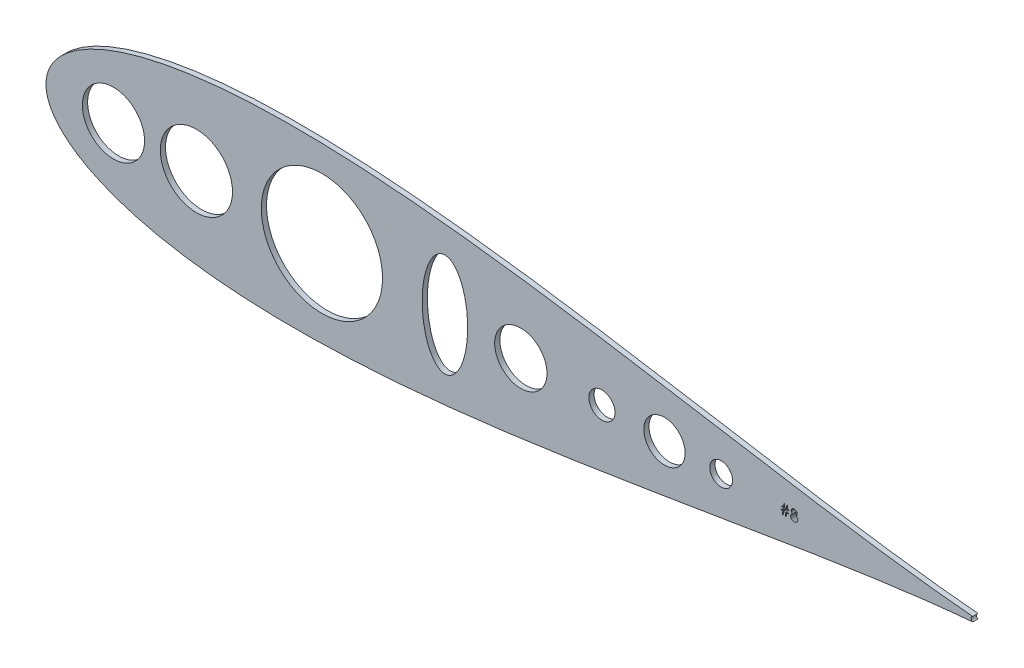
SolidWorks part; units mm, degrees
ref_plane "Front Plane" through (0, 0, 0) normal (0, 0, 1) x (1, 0, 0)
ref_plane "Top Plane" through (0, 0, 0) normal (0, 1, 0) x (1, 0, 0)
ref_plane "Right Plane" through (0, 0, 0) normal (1, 0, 0) x (0, 0, -1)
sketch "Model" plane through (0, 0, 0) normal (0, 0, 1) x (1, 0, 0)
  line L0 (694.3768, 545.3653) -> (694.3768, 545.0397)
  line L1 (694.3768, 545.0397) -> (693.406, 545.0397)
  line L2 (693.406, 545.0397) -> (693.1424, 543.2812)
  line L3 (693.1424, 543.2812) -> (692.7486, 543.2812)
  line L4 (692.7486, 543.2812) -> (693.0121, 545.0397)
  line L5 (693.0121, 545.0397) -> (691.9731, 545.0397)
  line L6 (691.9731, 545.0397) -> (691.7096, 543.2812)
  line L7 (691.7096, 543.2812) -> (691.3158, 543.2812)
  line L8 (691.3158, 543.2812) -> (691.5793, 545.0397)
  line L9 (691.5793, 545.0397) -> (690.7296, 545.0397)
  line L10 (690.7296, 545.0397) -> (690.7296, 545.3653)
  line L11 (690.7296, 545.3653) -> (691.6282, 545.3653)
  line L12 (691.6282, 545.3653) -> (691.8042, 546.5376)
  line L13 (691.8042, 546.5376) -> (690.8599, 546.5376)
  line L14 (690.8599, 546.5376) -> (690.8599, 546.8632)
  line L15 (690.8599, 546.8632) -> (691.8531, 546.8632)
  line L16 (691.8531, 546.8632) -> (692.0973, 548.4915)
  line L17 (692.0973, 548.4915) -> (692.4901, 548.4915)
  line L18 (692.4901, 548.4915) -> (692.2459, 546.8632)
  line L19 (692.2459, 546.8632) -> (693.2859, 546.8632)
  line L20 (693.2859, 546.8632) -> (693.5301, 548.4915)
  line L21 (693.5301, 548.4915) -> (693.9229, 548.4915)
  line L22 (693.9229, 548.4915) -> (693.6787, 546.8632)
  line L23 (693.6787, 546.8632) -> (694.507, 546.8632)
  line L24 (694.507, 546.8632) -> (694.507, 546.5376)
  line L25 (694.507, 546.5376) -> (693.6298, 546.5376)
  line L26 (693.6298, 546.5376) -> (693.4548, 545.3653)
  line L27 (693.4548, 545.3653) -> (694.3768, 545.3653)
  line L28 (693.237, 546.5376) -> (692.197, 546.5376)
  line L29 (692.197, 546.5376) -> (692.022, 545.3653)
  line L30 (692.022, 545.3653) -> (693.061, 545.3653)
  line L31 (693.061, 545.3653) -> (693.237, 546.5376)
  line L32 (697.8235, 546.1112) -> (697.9476, 546.0451)
  line L33 (697.9476, 546.0451) -> (698.0626, 545.9769)
  line L34 (698.0626, 545.9769) -> (698.1685, 545.9057)
  line L35 (698.1685, 545.9057) -> (698.2662, 545.8334)
  line L36 (698.2662, 545.8334) -> (698.3557, 545.7581)
  line L37 (698.3557, 545.7581) -> (698.4361, 545.6797)
  line L38 (698.4361, 545.6797) -> (698.5073, 545.6004)
  line L39 (698.5073, 545.6004) -> (698.5704, 545.5179)
  line L40 (698.5704, 545.5179) -> (698.6254, 545.4335)
  line L41 (698.6254, 545.4335) -> (698.6732, 545.346)
  line L42 (698.6732, 545.346) -> (698.7139, 545.2554)
  line L43 (698.7139, 545.2554) -> (698.7465, 545.1628)
  line L44 (698.7465, 545.1628) -> (698.7729, 545.0661)
  line L45 (698.7729, 545.0661) -> (698.7913, 544.9674)
  line L46 (698.7913, 544.9674) -> (698.8014, 544.8656)
  line L47 (698.8014, 544.8656) -> (698.8055, 544.7608)
  line L48 (698.8055, 544.7608) -> (698.7994, 544.6143)
  line L49 (698.7994, 544.6143) -> (698.7811, 544.4718)
  line L50 (698.7811, 544.4718) -> (698.7516, 544.3334)
  line L51 (698.7516, 544.3334) -> (698.7098, 544.2001)
  line L52 (698.7098, 544.2001) -> (698.6549, 544.0699)
  line L53 (698.6549, 544.0699) -> (698.5887, 543.9457)
  line L54 (698.5887, 543.9457) -> (698.5114, 543.8246)
  line L55 (698.5114, 543.8246) -> (698.4208, 543.7086)
  line L56 (698.4208, 543.7086) -> (698.2967, 543.5783)
  line L57 (698.2967, 543.5783) -> (698.1603, 543.4644)
  line L58 (698.1603, 543.4644) -> (698.0107, 543.3687)
  line L59 (698.0107, 543.3687) -> (697.8479, 543.2904)
  line L60 (697.8479, 543.2904) -> (697.6729, 543.2293)
  line L61 (697.6729, 543.2293) -> (697.4856, 543.1855)
  line L62 (697.4856, 543.1855) -> (697.2852, 543.1601)
  line L63 (697.2852, 543.1601) -> (697.0725, 543.1509)
  line L64 (697.0725, 543.1509) -> (696.8679, 543.1591)
  line L65 (696.8679, 543.1591) -> (696.6756, 543.1815)
  line L66 (696.6756, 543.1815) -> (696.4955, 543.2201)
  line L67 (696.4955, 543.2201) -> (696.3296, 543.2731)
  line L68 (696.3296, 543.2731) -> (696.1749, 543.3423)
  line L69 (696.1749, 543.3423) -> (696.0345, 543.4267)
  line L70 (696.0345, 543.4267) -> (695.9063, 543.5254)
  line L71 (695.9063, 543.5254) -> (695.7903, 543.6404)
  line L72 (695.7903, 543.6404) -> (695.6875, 543.7646)
  line L73 (695.6875, 543.7646) -> (695.599, 543.8918)
  line L74 (695.599, 543.8918) -> (695.5247, 544.022)
  line L75 (695.5247, 544.022) -> (695.4626, 544.1553)
  line L76 (695.4626, 544.1553) -> (695.4148, 544.2917)
  line L77 (695.4148, 544.2917) -> (695.3812, 544.4311)
  line L78 (695.3812, 544.4311) -> (695.3608, 544.5736)
  line L79 (695.3608, 544.5736) -> (695.3537, 544.7191)
  line L80 (695.3537, 544.7191) -> (695.3578, 544.826)
  line L81 (695.3578, 544.826) -> (695.369, 544.9298)
  line L82 (695.369, 544.9298) -> (695.3873, 545.0305)
  line L83 (695.3873, 545.0305) -> (695.4127, 545.1292)
  line L84 (695.4127, 545.1292) -> (695.4463, 545.2249)
  line L85 (695.4463, 545.2249) -> (695.487, 545.3175)
  line L86 (695.487, 545.3175) -> (695.5348, 545.408)
  line L87 (695.5348, 545.408) -> (695.5898, 545.4956)
  line L88 (695.5898, 545.4956) -> (695.6539, 545.581)
  line L89 (695.6539, 545.581) -> (695.7262, 545.6635)
  line L90 (695.7262, 545.6635) -> (695.8086, 545.7439)
  line L91 (695.8086, 545.7439) -> (695.9002, 545.8222)
  line L92 (695.9002, 545.8222) -> (695.9999, 545.8985)
  line L93 (695.9999, 545.8985) -> (696.1098, 545.9718)
  line L94 (696.1098, 545.9718) -> (696.2279, 546.043)
  line L95 (696.2279, 546.043) -> (696.3561, 546.1112)
  line L96 (696.3561, 546.1112) -> (696.1821, 546.212)
  line L97 (696.1821, 546.212) -> (696.0314, 546.3249)
  line L98 (696.0314, 546.3249) -> (695.9042, 546.4481)
  line L99 (695.9042, 546.4481) -> (695.7994, 546.5834)
  line L100 (695.7994, 546.5834) -> (695.718, 546.7269)
  line L101 (695.718, 546.7269) -> (695.661, 546.8755)
  line L102 (695.661, 546.8755) -> (695.6254, 547.0291)
  line L103 (695.6254, 547.0291) -> (695.6142, 547.1879)
  line L104 (695.6142, 547.1879) -> (695.6264, 547.3497)
  line L105 (695.6264, 547.3497) -> (695.6631, 547.5094)
  line L106 (695.6631, 547.5094) -> (695.7251, 547.6682)
  line L107 (695.7251, 547.6682) -> (695.8106, 547.8239)
  line L108 (695.8106, 547.8239) -> (695.9185, 547.9714)
  line L109 (695.9185, 547.9714) -> (696.0447, 548.1017)
  line L110 (696.0447, 548.1017) -> (696.1892, 548.2157)
  line L111 (696.1892, 548.2157) -> (696.353, 548.3134)
  line L112 (696.353, 548.3134) -> (696.5301, 548.3917)
  line L113 (696.5301, 548.3917) -> (696.7143, 548.4467)
  line L114 (696.7143, 548.4467) -> (696.9046, 548.4803)
  line L115 (696.9046, 548.4803) -> (697.103, 548.4915)
  line L116 (697.103, 548.4915) -> (697.2964, 548.4803)
  line L117 (697.2964, 548.4803) -> (697.4816, 548.4467)
  line L118 (697.4816, 548.4467) -> (697.6597, 548.3897)
  line L119 (697.6597, 548.3897) -> (697.8306, 548.3113)
  line L120 (697.8306, 548.3113) -> (697.9894, 548.2136)
  line L121 (697.9894, 548.2136) -> (698.1288, 548.0986)
  line L122 (698.1288, 548.0986) -> (698.2509, 547.9684)
  line L123 (698.2509, 547.9684) -> (698.3547, 547.8219)
  line L124 (698.3547, 547.8219) -> (698.4381, 547.6662)
  line L125 (698.4381, 547.6662) -> (698.4972, 547.5054)
  line L126 (698.4972, 547.5054) -> (698.5328, 547.3415)
  line L127 (698.5328, 547.3415) -> (698.545, 547.1736)
  line L128 (698.545, 547.1736) -> (698.5338, 547.0088)
  line L129 (698.5338, 547.0088) -> (698.5002, 546.8531)
  line L130 (698.5002, 546.8531) -> (698.4432, 546.7065)
  line L131 (698.4432, 546.7065) -> (698.3649, 546.5692)
  line L132 (698.3649, 546.5692) -> (698.2631, 546.4409)
  line L133 (698.2631, 546.4409) -> (698.14, 546.3229)
  line L134 (698.14, 546.3229) -> (697.9924, 546.212)
  line L135 (697.9924, 546.212) -> (697.8235, 546.1112)
  line L136 (697.0776, 547.9704) -> (696.9707, 547.9664)
  line L137 (696.9707, 547.9664) -> (696.869, 547.9562)
  line L138 (696.869, 547.9562) -> (696.7723, 547.9379)
  line L139 (696.7723, 547.9379) -> (696.6797, 547.9124)
  line L140 (696.6797, 547.9124) -> (696.5911, 547.8788)
  line L141 (696.5911, 547.8788) -> (696.5087, 547.8392)
  line L142 (696.5087, 547.8392) -> (696.4304, 547.7913)
  line L143 (696.4304, 547.7913) -> (696.3561, 547.7364)
  line L144 (696.3561, 547.7364) -> (696.2889, 547.6763)
  line L145 (696.2889, 547.6763) -> (696.2309, 547.6143)
  line L146 (696.2309, 547.6143) -> (696.1821, 547.5491)
  line L147 (696.1821, 547.5491) -> (696.1414, 547.4809)
  line L148 (696.1414, 547.4809) -> (696.1108, 547.4097)
  line L149 (696.1108, 547.4097) -> (696.0884, 547.3364)
  line L150 (696.0884, 547.3364) -> (696.0742, 547.2601)
  line L151 (696.0742, 547.2601) -> (696.0701, 547.1807)
  line L152 (696.0701, 547.1807) -> (696.0752, 547.1014)
  line L153 (696.0752, 547.1014) -> (696.0895, 547.0251)
  line L154 (696.0895, 547.0251) -> (696.1129, 546.9497)
  line L155 (696.1129, 546.9497) -> (696.1475, 546.8765)
  line L156 (696.1475, 546.8765) -> (696.1902, 546.8052)
  line L157 (696.1902, 546.8052) -> (696.2431, 546.735)
  line L158 (696.2431, 546.735) -> (696.3052, 546.6679)
  line L159 (696.3052, 546.6679) -> (696.3774, 546.6017)
  line L160 (696.3774, 546.6017) -> (696.4558, 546.5407)
  line L161 (696.4558, 546.5407) -> (696.5382, 546.4877)
  line L162 (696.5382, 546.4877) -> (696.6227, 546.444)
  line L163 (696.6227, 546.444) -> (696.7112, 546.4074)
  line L164 (696.7112, 546.4074) -> (696.8028, 546.3789)
  line L165 (696.8028, 546.3789) -> (696.8974, 546.3585)
  line L166 (696.8974, 546.3585) -> (696.9951, 546.3463)
  line L167 (696.9951, 546.3463) -> (697.0959, 546.3422)
  line L168 (697.0959, 546.3422) -> (697.2251, 546.3493)
  line L169 (697.2251, 546.3493) -> (697.3513, 546.3717)
  line L170 (697.3513, 546.3717) -> (697.4734, 546.4084)
  line L171 (697.4734, 546.4084) -> (697.5925, 546.4592)
  line L172 (697.5925, 546.4592) -> (697.7034, 546.5234)
  line L173 (697.7034, 546.5234) -> (697.8011, 546.5987)
  line L174 (697.8011, 546.5987) -> (697.8856, 546.6841)
  line L175 (697.8856, 546.6841) -> (697.9578, 546.7808)
  line L176 (697.9578, 546.7808) -> (698.0148, 546.8836)
  line L177 (698.0148, 546.8836) -> (698.0565, 546.9854)
  line L178 (698.0565, 546.9854) -> (698.081, 547.0881)
  line L179 (698.081, 547.0881) -> (698.0891, 547.1909)
  line L180 (698.0891, 547.1909) -> (698.085, 547.2632)
  line L181 (698.085, 547.2632) -> (698.0728, 547.3334)
  line L182 (698.0728, 547.3334) -> (698.0525, 547.4016)
  line L183 (698.0525, 547.4016) -> (698.024, 547.4698)
  line L184 (698.024, 547.4698) -> (697.9873, 547.5359)
  line L185 (697.9873, 547.5359) -> (697.9436, 547.6)
  line L186 (697.9436, 547.6) -> (697.8907, 547.6631)
  line L187 (697.8907, 547.6631) -> (697.8296, 547.7252)
  line L188 (697.8296, 547.7252) -> (697.7614, 547.7822)
  line L189 (697.7614, 547.7822) -> (697.6861, 547.832)
  line L190 (697.6861, 547.832) -> (697.6027, 547.8748)
  line L191 (697.6027, 547.8748) -> (697.5121, 547.9094)
  line L192 (697.5121, 547.9094) -> (697.4144, 547.9358)
  line L193 (697.4144, 547.9358) -> (697.3096, 547.9552)
  line L194 (697.3096, 547.9552) -> (697.1977, 547.9664)
  line L195 (697.1977, 547.9664) -> (697.0776, 547.9704)
  line L196 (697.1071, 545.8212) -> (696.9717, 545.8161)
  line L197 (696.9717, 545.8161) -> (696.8425, 545.7998)
  line L198 (696.8425, 545.7998) -> (696.7183, 545.7744)
  line L199 (696.7183, 545.7744) -> (696.6003, 545.7378)
  line L200 (696.6003, 545.7378) -> (696.4873, 545.6899)
  line L201 (696.4873, 545.6899) -> (696.3795, 545.6319)
  line L202 (696.3795, 545.6319) -> (696.2777, 545.5637)
  line L203 (696.2777, 545.5637) -> (696.1821, 545.4854)
  line L204 (696.1821, 545.4854) -> (696.0945, 545.3999)
  line L205 (696.0945, 545.3999) -> (696.0192, 545.3114)
  line L206 (696.0192, 545.3114) -> (695.9551, 545.2188)
  line L207 (695.9551, 545.2188) -> (695.9032, 545.1231)
  line L208 (695.9032, 545.1231) -> (695.8615, 545.0234)
  line L209 (695.8615, 545.0234) -> (695.833, 544.9206)
  line L210 (695.833, 544.9206) -> (695.8157, 544.8137)
  line L211 (695.8157, 544.8137) -> (695.8096, 544.7038)
  line L212 (695.8096, 544.7038) -> (695.8198, 544.5675)
  line L213 (695.8198, 544.5675) -> (695.8493, 544.4362)
  line L214 (695.8493, 544.4362) -> (695.8992, 544.307)
  line L215 (695.8992, 544.307) -> (695.9684, 544.1828)
  line L216 (695.9684, 544.1828) -> (696.0559, 544.0668)
  line L217 (696.0559, 544.0668) -> (696.1597, 543.9661)
  line L218 (696.1597, 543.9661) -> (696.2787, 543.8775)
  line L219 (696.2787, 543.8775) -> (696.4141, 543.8043)
  line L220 (696.4141, 543.8043) -> (696.5637, 543.7463)
  line L221 (696.5637, 543.7463) -> (696.7234, 543.7055)
  line L222 (696.7234, 543.7055) -> (696.8954, 543.6801)
  line L223 (696.8954, 543.6801) -> (697.0776, 543.672)
  line L224 (697.0776, 543.672) -> (697.22, 543.6771)
  line L225 (697.22, 543.6771) -> (697.3544, 543.6923)
  line L226 (697.3544, 543.6923) -> (697.4816, 543.7178)
  line L227 (697.4816, 543.7178) -> (697.6006, 543.7534)
  line L228 (697.6006, 543.7534) -> (697.7126, 543.7982)
  line L229 (697.7126, 543.7982) -> (697.8174, 543.8541)
  line L230 (697.8174, 543.8541) -> (697.9151, 543.9192)
  line L231 (697.9151, 543.9192) -> (698.0046, 543.9956)
  line L232 (698.0046, 543.9956) -> (698.085, 544.078)
  line L233 (698.085, 544.078) -> (698.1552, 544.1645)
  line L234 (698.1552, 544.1645) -> (698.2153, 544.254)
  line L235 (698.2153, 544.254) -> (698.2631, 544.3467)
  line L236 (698.2631, 544.3467) -> (698.3008, 544.4423)
  line L237 (698.3008, 544.4423) -> (698.3282, 544.542)
  line L238 (698.3282, 544.542) -> (698.3445, 544.6448)
  line L239 (698.3445, 544.6448) -> (698.3496, 544.7517)
  line L240 (698.3496, 544.7517) -> (698.3435, 544.8555)
  line L241 (698.3435, 544.8555) -> (698.3272, 544.9552)
  line L242 (698.3272, 544.9552) -> (698.2987, 545.0529)
  line L243 (698.2987, 545.0529) -> (698.259, 545.1475)
  line L244 (698.259, 545.1475) -> (698.2071, 545.2391)
  line L245 (698.2071, 545.2391) -> (698.1451, 545.3276)
  line L246 (698.1451, 545.3276) -> (698.0708, 545.4131)
  line L247 (698.0708, 545.4131) -> (697.9853, 545.4956)
  line L248 (697.9853, 545.4956) -> (697.8917, 545.5719)
  line L249 (697.8917, 545.5719) -> (697.794, 545.638)
  line L250 (697.794, 545.638) -> (697.6912, 545.694)
  line L251 (697.6912, 545.694) -> (697.5833, 545.7398)
  line L252 (697.5833, 545.7398) -> (697.4714, 545.7754)
  line L253 (697.4714, 545.7754) -> (697.3544, 545.8008)
  line L254 (697.3544, 545.8008) -> (697.2333, 545.8161)
  line L255 (697.2333, 545.8161) -> (697.1071, 545.8212)
  circle A0 centre (406.8977, 545.5348) radius 17.526
  circle A1 centre (366.6463, 545.5348) radius 15.0914
  circle A2 centre (564.3777, 545.5348) radius 12.7
  circle A3 centre (603.7477, 545.5348) radius 6.35
  circle A4 centre (467.8255, 545.5348) radius 29.4326
  circle A5 centre (634.0834, 545.5348) radius 10.0345
  circle A6 centre (661.6144, 545.5348) radius 5.5299
  arc A7 (783.748, 546.6896) -> (783.7459, 544.3797) centre (784.2108, 545.5343) ccw
  ellipse E0 centre (527.5368, 545.5348) end of major axis (527.5368, 520.5466) minor radius 11.0619
  spline S0 degree 3 poles (783.748, 546.6896) (783.5679, 546.7048) (781.0177, 546.921) (775.8156, 547.4018) (767.8244, 548.2331) (758.9644, 549.2532) (749.2688, 550.4682) (738.7829, 551.8793) (727.5521, 553.4834) (715.6249, 555.2721) (703.0521, 557.2329) (689.8862, 559.3481) (676.1817, 561.5959) (661.9946, 563.9503) (647.3823, 566.3818) (632.4035, 568.8573) (617.118, 571.3408) (601.5869, 573.7944) (585.8723, 576.1779) (570.0376, 578.4505) (554.1471, 580.5706) (538.2663, 582.4969) (522.462, 584.1888) (506.8018, 585.6072) (491.3548, 586.7151) (476.191, 587.4785) (461.3816, 587.8664) (446.999, 587.852) (433.1165, 587.4124) (419.8088, 586.5305) (407.1517, 585.1934) (395.2225, 583.395) (384.1009, 581.1349) (373.8692, 578.4205) (364.6137, 575.2677) (356.4268, 571.7046) (349.408, 567.7785) (343.6622, 563.569) (339.286, 559.2135) (336.3232, 554.9424) (334.6711, 551.0891) (334.0039, 547.9979) (333.852, 545.5348) (334.0039, 543.0716) (334.6711, 539.9805) (336.3232, 536.1271) (339.286, 531.856) (343.6622, 527.5006) (349.408, 523.291) (356.4268, 519.3649) (364.6137, 515.8019) (373.8692, 512.6491) (384.1009, 509.9347) (395.2225, 507.6745) (407.1517, 505.8762) (419.8088, 504.5391) (433.1165, 503.6571) (446.999, 503.2175) (461.3816, 503.2031) (476.191, 503.5911) (491.3548, 504.3544) (506.8018, 505.4624) (522.462, 506.8808) (538.2663, 508.5726) (554.1471, 510.4989) (570.0376, 512.619) (585.8723, 514.8916) (601.5869, 517.2752) (617.118, 519.7287) (632.4035, 522.2123) (647.3823, 524.6877) (661.9946, 527.1192) (676.1817, 529.4737) (689.8862, 531.7215) (703.0521, 533.8367) (715.6249, 535.7974) (727.5521, 537.5862) (738.7829, 539.1903) (749.2688, 540.6014) (758.9644, 541.8164) (767.8244, 542.8364) (775.8156, 543.6677) (781.017, 544.1485) (783.5665, 544.3646) (783.7459, 544.3797) knots 0.020718 0.020718 0.020718 0.020718 0.021271 0.028553 0.036781 0.04592 0.055932 0.066773 0.078397 0.090755 0.103793 0.117456 0.131686 0.146422 0.1616 0.177156 0.193024 0.209135 0.225421 0.241812 0.258238 0.274629 0.290914 0.307025 0.322893 0.338448 0.353626 0.368361 0.38259 0.396253 0.40929 0.421647 0.43327 0.444109 0.454119 0.463255 0.471479 0.478755 0.485052 0.490344 0.49461 0.497833 0.5 0.502167 0.50539 0.509656 0.514948 0.521245 0.528521 0.536745 0.545881 0.555891 0.56673 0.578353 0.59071 0.603747 0.61741 0.631639 0.646374 0.661552 0.677107 0.692975 0.709086 0.725371 0.741762 0.758188 0.774579 0.790865 0.806976 0.822844 0.8384 0.853578 0.868314 0.882544 0.896207 0.909245 0.921603 0.933227 0.944068 0.95408 0.963219 0.971447 0.978729 0.97928 0.97928 0.97928 0.97928
sketch "Sketch2" plane through (0, 0, 0) normal (0, 0, 1) x (1, 0, 0)
  line L0 (694.3768, 545.3653) -> (694.3768, 545.0397)
  line L1 (694.3768, 545.0397) -> (693.406, 545.0397)
  line L2 (693.406, 545.0397) -> (693.1424, 543.2812)
  line L3 (693.1424, 543.2812) -> (692.7486, 543.2812)
  line L4 (692.7486, 543.2812) -> (693.0121, 545.0397)
  line L5 (693.0121, 545.0397) -> (691.9731, 545.0397)
  line L6 (691.9731, 545.0397) -> (691.7096, 543.2812)
  line L7 (691.7096, 543.2812) -> (691.3158, 543.2812)
  line L8 (691.3158, 543.2812) -> (691.5793, 545.0397)
  line L9 (691.5793, 545.0397) -> (690.7296, 545.0397)
  line L10 (690.7296, 545.0397) -> (690.7296, 545.3653)
  line L11 (690.7296, 545.3653) -> (691.6282, 545.3653)
  line L12 (691.6282, 545.3653) -> (691.8042, 546.5376)
  line L13 (691.8042, 546.5376) -> (690.8599, 546.5376)
  line L14 (690.8599, 546.5376) -> (690.8599, 546.8632)
  line L15 (690.8599, 546.8632) -> (691.8531, 546.8632)
  line L16 (691.8531, 546.8632) -> (692.0973, 548.4915)
  line L17 (692.0973, 548.4915) -> (692.4901, 548.4915)
  line L18 (692.4901, 548.4915) -> (692.2459, 546.8632)
  line L19 (692.2459, 546.8632) -> (693.2859, 546.8632)
  line L20 (693.2859, 546.8632) -> (693.5301, 548.4915)
  line L21 (693.5301, 548.4915) -> (693.9229, 548.4915)
  line L22 (693.9229, 548.4915) -> (693.6787, 546.8632)
  line L23 (693.6787, 546.8632) -> (694.507, 546.8632)
  line L24 (694.507, 546.8632) -> (694.507, 546.5376)
  line L25 (694.507, 546.5376) -> (693.6298, 546.5376)
  line L26 (693.6298, 546.5376) -> (693.4548, 545.3653)
  line L27 (693.4548, 545.3653) -> (694.3768, 545.3653)
  line L28 (693.237, 546.5376) -> (692.197, 546.5376)
  line L29 (692.197, 546.5376) -> (692.022, 545.3653)
  line L30 (692.022, 545.3653) -> (693.061, 545.3653)
  line L31 (693.061, 545.3653) -> (693.237, 546.5376)
  line L32 (697.8235, 546.1112) -> (697.9476, 546.0451)
  line L33 (697.9476, 546.0451) -> (698.0626, 545.9769)
  line L34 (698.0626, 545.9769) -> (698.1685, 545.9057)
  line L35 (698.1685, 545.9057) -> (698.2662, 545.8334)
  line L36 (698.2662, 545.8334) -> (698.3557, 545.7581)
  line L37 (698.3557, 545.7581) -> (698.4361, 545.6797)
  line L38 (698.4361, 545.6797) -> (698.5073, 545.6004)
  line L39 (698.5073, 545.6004) -> (698.5704, 545.5179)
  line L40 (698.5704, 545.5179) -> (698.6254, 545.4335)
  line L41 (698.6254, 545.4335) -> (698.6732, 545.346)
  line L42 (698.6732, 545.346) -> (698.7139, 545.2554)
  line L43 (698.7139, 545.2554) -> (698.7465, 545.1628)
  line L44 (698.7465, 545.1628) -> (698.7729, 545.0661)
  line L45 (698.7729, 545.0661) -> (698.7913, 544.9674)
  line L46 (698.7913, 544.9674) -> (698.8014, 544.8656)
  line L47 (698.8014, 544.8656) -> (698.8055, 544.7608)
  line L48 (698.8055, 544.7608) -> (698.7994, 544.6143)
  line L49 (698.7994, 544.6143) -> (698.7811, 544.4718)
  line L50 (698.7811, 544.4718) -> (698.7516, 544.3334)
  line L51 (698.7516, 544.3334) -> (698.7098, 544.2001)
  line L52 (698.7098, 544.2001) -> (698.6549, 544.0699)
  line L53 (698.6549, 544.0699) -> (698.5887, 543.9457)
  line L54 (698.5887, 543.9457) -> (698.5114, 543.8246)
  line L55 (698.5114, 543.8246) -> (698.4208, 543.7086)
  line L56 (698.4208, 543.7086) -> (698.2967, 543.5783)
  line L57 (698.2967, 543.5783) -> (698.1603, 543.4644)
  line L58 (698.1603, 543.4644) -> (698.0107, 543.3687)
  line L59 (698.0107, 543.3687) -> (697.8479, 543.2904)
  line L60 (697.8479, 543.2904) -> (697.6729, 543.2293)
  line L61 (697.6729, 543.2293) -> (697.4856, 543.1855)
  line L62 (697.4856, 543.1855) -> (697.2852, 543.1601)
  line L63 (697.2852, 543.1601) -> (697.0725, 543.1509)
  line L64 (697.0725, 543.1509) -> (696.8679, 543.1591)
  line L65 (696.8679, 543.1591) -> (696.6756, 543.1815)
  line L66 (696.6756, 543.1815) -> (696.4955, 543.2201)
  line L67 (696.4955, 543.2201) -> (696.3296, 543.2731)
  line L68 (696.3296, 543.2731) -> (696.1749, 543.3423)
  line L69 (696.1749, 543.3423) -> (696.0345, 543.4267)
  line L70 (696.0345, 543.4267) -> (695.9063, 543.5254)
  line L71 (695.9063, 543.5254) -> (695.7903, 543.6404)
  line L72 (695.7903, 543.6404) -> (695.6875, 543.7646)
  line L73 (695.6875, 543.7646) -> (695.599, 543.8918)
  line L74 (695.599, 543.8918) -> (695.5247, 544.022)
  line L75 (695.5247, 544.022) -> (695.4626, 544.1553)
  line L76 (695.4626, 544.1553) -> (695.4148, 544.2917)
  line L77 (695.4148, 544.2917) -> (695.3812, 544.4311)
  line L78 (695.3812, 544.4311) -> (695.3608, 544.5736)
  line L79 (695.3608, 544.5736) -> (695.3537, 544.7191)
  line L80 (695.3537, 544.7191) -> (695.3578, 544.826)
  line L81 (695.3578, 544.826) -> (695.369, 544.9298)
  line L82 (695.369, 544.9298) -> (695.3873, 545.0305)
  line L83 (695.3873, 545.0305) -> (695.4127, 545.1292)
  line L84 (695.4127, 545.1292) -> (695.4463, 545.2249)
  line L85 (695.4463, 545.2249) -> (695.487, 545.3175)
  line L86 (695.487, 545.3175) -> (695.5348, 545.408)
  line L87 (695.5348, 545.408) -> (695.5898, 545.4956)
  line L88 (695.5898, 545.4956) -> (695.6539, 545.581)
  line L89 (695.6539, 545.581) -> (695.7262, 545.6635)
  line L90 (695.7262, 545.6635) -> (695.8086, 545.7439)
  line L91 (695.8086, 545.7439) -> (695.9002, 545.8222)
  line L92 (695.9002, 545.8222) -> (695.9999, 545.8985)
  line L93 (695.9999, 545.8985) -> (696.1098, 545.9718)
  line L94 (696.1098, 545.9718) -> (696.2279, 546.043)
  line L95 (696.2279, 546.043) -> (696.3561, 546.1112)
  line L96 (696.3561, 546.1112) -> (696.1821, 546.212)
  line L97 (696.1821, 546.212) -> (696.0314, 546.3249)
  line L98 (696.0314, 546.3249) -> (695.9042, 546.4481)
  line L99 (695.9042, 546.4481) -> (695.7994, 546.5834)
  line L100 (695.7994, 546.5834) -> (695.718, 546.7269)
  line L101 (695.718, 546.7269) -> (695.661, 546.8755)
  line L102 (695.661, 546.8755) -> (695.6254, 547.0291)
  line L103 (695.6254, 547.0291) -> (695.6142, 547.1879)
  line L104 (695.6142, 547.1879) -> (695.6264, 547.3497)
  line L105 (695.6264, 547.3497) -> (695.6631, 547.5094)
  line L106 (695.6631, 547.5094) -> (695.7251, 547.6682)
  line L107 (695.7251, 547.6682) -> (695.8106, 547.8239)
  line L108 (695.8106, 547.8239) -> (695.9185, 547.9714)
  line L109 (695.9185, 547.9714) -> (696.0447, 548.1017)
  line L110 (696.0447, 548.1017) -> (696.1892, 548.2157)
  line L111 (696.1892, 548.2157) -> (696.353, 548.3134)
  line L112 (696.353, 548.3134) -> (696.5301, 548.3917)
  line L113 (696.5301, 548.3917) -> (696.7143, 548.4467)
  line L114 (696.7143, 548.4467) -> (696.9046, 548.4803)
  line L115 (696.9046, 548.4803) -> (697.103, 548.4915)
  line L116 (697.103, 548.4915) -> (697.2964, 548.4803)
  line L117 (697.2964, 548.4803) -> (697.4816, 548.4467)
  line L118 (697.4816, 548.4467) -> (697.6597, 548.3897)
  line L119 (697.6597, 548.3897) -> (697.8306, 548.3113)
  line L120 (697.8306, 548.3113) -> (697.9894, 548.2136)
  line L121 (697.9894, 548.2136) -> (698.1288, 548.0986)
  line L122 (698.1288, 548.0986) -> (698.2509, 547.9684)
  line L123 (698.2509, 547.9684) -> (698.3547, 547.8219)
  line L124 (698.3547, 547.8219) -> (698.4381, 547.6662)
  line L125 (698.4381, 547.6662) -> (698.4972, 547.5054)
  line L126 (698.4972, 547.5054) -> (698.5328, 547.3415)
  line L127 (698.5328, 547.3415) -> (698.545, 547.1736)
  line L128 (698.545, 547.1736) -> (698.5338, 547.0088)
  line L129 (698.5338, 547.0088) -> (698.5002, 546.8531)
  line L130 (698.5002, 546.8531) -> (698.4432, 546.7065)
  line L131 (698.4432, 546.7065) -> (698.3649, 546.5692)
  line L132 (698.3649, 546.5692) -> (698.2631, 546.4409)
  line L133 (698.2631, 546.4409) -> (698.14, 546.3229)
  line L134 (698.14, 546.3229) -> (697.9924, 546.212)
  line L135 (697.9924, 546.212) -> (697.8235, 546.1112)
  line L136 (697.0776, 547.9704) -> (696.9707, 547.9664)
  line L137 (696.9707, 547.9664) -> (696.869, 547.9562)
  line L138 (696.869, 547.9562) -> (696.7723, 547.9379)
  line L139 (696.7723, 547.9379) -> (696.6797, 547.9124)
  line L140 (696.6797, 547.9124) -> (696.5911, 547.8788)
  line L141 (696.5911, 547.8788) -> (696.5087, 547.8392)
  line L142 (696.5087, 547.8392) -> (696.4304, 547.7913)
  line L143 (696.4304, 547.7913) -> (696.3561, 547.7364)
  line L144 (696.3561, 547.7364) -> (696.2889, 547.6763)
  line L145 (696.2889, 547.6763) -> (696.2309, 547.6143)
  line L146 (696.2309, 547.6143) -> (696.1821, 547.5491)
  line L147 (696.1821, 547.5491) -> (696.1414, 547.4809)
  line L148 (696.1414, 547.4809) -> (696.1108, 547.4097)
  line L149 (696.1108, 547.4097) -> (696.0884, 547.3364)
  line L150 (696.0884, 547.3364) -> (696.0742, 547.2601)
  line L151 (696.0742, 547.2601) -> (696.0701, 547.1807)
  line L152 (696.0701, 547.1807) -> (696.0752, 547.1014)
  line L153 (696.0752, 547.1014) -> (696.0895, 547.0251)
  line L154 (696.0895, 547.0251) -> (696.1129, 546.9497)
  line L155 (696.1129, 546.9497) -> (696.1475, 546.8765)
  line L156 (696.1475, 546.8765) -> (696.1902, 546.8052)
  line L157 (696.1902, 546.8052) -> (696.2431, 546.735)
  line L158 (696.2431, 546.735) -> (696.3052, 546.6679)
  line L159 (696.3052, 546.6679) -> (696.3774, 546.6017)
  line L160 (696.3774, 546.6017) -> (696.4558, 546.5407)
  line L161 (696.4558, 546.5407) -> (696.5382, 546.4877)
  line L162 (696.5382, 546.4877) -> (696.6227, 546.444)
  line L163 (696.6227, 546.444) -> (696.7112, 546.4074)
  line L164 (696.7112, 546.4074) -> (696.8028, 546.3789)
  line L165 (696.8028, 546.3789) -> (696.8974, 546.3585)
  line L166 (696.8974, 546.3585) -> (696.9951, 546.3463)
  line L167 (696.9951, 546.3463) -> (697.0959, 546.3422)
  line L168 (697.0959, 546.3422) -> (697.2251, 546.3493)
  line L169 (697.2251, 546.3493) -> (697.3513, 546.3717)
  line L170 (697.3513, 546.3717) -> (697.4734, 546.4084)
  line L171 (697.4734, 546.4084) -> (697.5925, 546.4592)
  line L172 (697.5925, 546.4592) -> (697.7034, 546.5234)
  line L173 (697.7034, 546.5234) -> (697.8011, 546.5987)
  line L174 (697.8011, 546.5987) -> (697.8856, 546.6841)
  line L175 (697.8856, 546.6841) -> (697.9578, 546.7808)
  line L176 (697.9578, 546.7808) -> (698.0148, 546.8836)
  line L177 (698.0148, 546.8836) -> (698.0565, 546.9854)
  line L178 (698.0565, 546.9854) -> (698.081, 547.0881)
  line L179 (698.081, 547.0881) -> (698.0891, 547.1909)
  line L180 (698.0891, 547.1909) -> (698.085, 547.2632)
  line L181 (698.085, 547.2632) -> (698.0728, 547.3334)
  line L182 (698.0728, 547.3334) -> (698.0525, 547.4016)
  line L183 (698.0525, 547.4016) -> (698.024, 547.4698)
  line L184 (698.024, 547.4698) -> (697.9873, 547.5359)
  line L185 (697.9873, 547.5359) -> (697.9436, 547.6)
  line L186 (697.9436, 547.6) -> (697.8907, 547.6631)
  line L187 (697.8907, 547.6631) -> (697.8296, 547.7252)
  line L188 (697.8296, 547.7252) -> (697.7614, 547.7822)
  line L189 (697.7614, 547.7822) -> (697.6861, 547.832)
  line L190 (697.6861, 547.832) -> (697.6027, 547.8748)
  line L191 (697.6027, 547.8748) -> (697.5121, 547.9094)
  line L192 (697.5121, 547.9094) -> (697.4144, 547.9358)
  line L193 (697.4144, 547.9358) -> (697.3096, 547.9552)
  line L194 (697.3096, 547.9552) -> (697.1977, 547.9664)
  line L195 (697.1977, 547.9664) -> (697.0776, 547.9704)
  line L196 (697.1071, 545.8212) -> (696.9717, 545.8161)
  line L197 (696.9717, 545.8161) -> (696.8425, 545.7998)
  line L198 (696.8425, 545.7998) -> (696.7183, 545.7744)
  line L199 (696.7183, 545.7744) -> (696.6003, 545.7378)
  line L200 (696.6003, 545.7378) -> (696.4873, 545.6899)
  line L201 (696.4873, 545.6899) -> (696.3795, 545.6319)
  line L202 (696.3795, 545.6319) -> (696.2777, 545.5637)
  line L203 (696.2777, 545.5637) -> (696.1821, 545.4854)
  line L204 (696.1821, 545.4854) -> (696.0945, 545.3999)
  line L205 (696.0945, 545.3999) -> (696.0192, 545.3114)
  line L206 (696.0192, 545.3114) -> (695.9551, 545.2188)
  line L207 (695.9551, 545.2188) -> (695.9032, 545.1231)
  line L208 (695.9032, 545.1231) -> (695.8615, 545.0234)
  line L209 (695.8615, 545.0234) -> (695.833, 544.9206)
  line L210 (695.833, 544.9206) -> (695.8157, 544.8137)
  line L211 (695.8157, 544.8137) -> (695.8096, 544.7038)
  line L212 (695.8096, 544.7038) -> (695.8198, 544.5675)
  line L213 (695.8198, 544.5675) -> (695.8493, 544.4362)
  line L214 (695.8493, 544.4362) -> (695.8992, 544.307)
  line L215 (695.8992, 544.307) -> (695.9684, 544.1828)
  line L216 (695.9684, 544.1828) -> (696.0559, 544.0668)
  line L217 (696.0559, 544.0668) -> (696.1597, 543.9661)
  line L218 (696.1597, 543.9661) -> (696.2787, 543.8775)
  line L219 (696.2787, 543.8775) -> (696.4141, 543.8043)
  line L220 (696.4141, 543.8043) -> (696.5637, 543.7463)
  line L221 (696.5637, 543.7463) -> (696.7234, 543.7055)
  line L222 (696.7234, 543.7055) -> (696.8954, 543.6801)
  line L223 (696.8954, 543.6801) -> (697.0776, 543.672)
  line L224 (697.0776, 543.672) -> (697.22, 543.6771)
  line L225 (697.22, 543.6771) -> (697.3544, 543.6923)
  line L226 (697.3544, 543.6923) -> (697.4816, 543.7178)
  line L227 (697.4816, 543.7178) -> (697.6006, 543.7534)
  line L228 (697.6006, 543.7534) -> (697.7126, 543.7982)
  line L229 (697.7126, 543.7982) -> (697.8174, 543.8541)
  line L230 (697.8174, 543.8541) -> (697.9151, 543.9192)
  line L231 (697.9151, 543.9192) -> (698.0046, 543.9956)
  line L232 (698.0046, 543.9956) -> (698.085, 544.078)
  line L233 (698.085, 544.078) -> (698.1552, 544.1645)
  line L234 (698.1552, 544.1645) -> (698.2153, 544.254)
  line L235 (698.2153, 544.254) -> (698.2631, 544.3467)
  line L236 (698.2631, 544.3467) -> (698.3008, 544.4423)
  line L237 (698.3008, 544.4423) -> (698.3282, 544.542)
  line L238 (698.3282, 544.542) -> (698.3445, 544.6448)
  line L239 (698.3445, 544.6448) -> (698.3496, 544.7517)
  line L240 (698.3496, 544.7517) -> (698.3435, 544.8555)
  line L241 (698.3435, 544.8555) -> (698.3272, 544.9552)
  line L242 (698.3272, 544.9552) -> (698.2987, 545.0529)
  line L243 (698.2987, 545.0529) -> (698.259, 545.1475)
  line L244 (698.259, 545.1475) -> (698.2071, 545.2391)
  line L245 (698.2071, 545.2391) -> (698.1451, 545.3276)
  line L246 (698.1451, 545.3276) -> (698.0708, 545.4131)
  line L247 (698.0708, 545.4131) -> (697.9853, 545.4956)
  line L248 (697.9853, 545.4956) -> (697.8917, 545.5719)
  line L249 (697.8917, 545.5719) -> (697.794, 545.638)
  line L250 (697.794, 545.638) -> (697.6912, 545.694)
  line L251 (697.6912, 545.694) -> (697.5833, 545.7398)
  line L252 (697.5833, 545.7398) -> (697.4714, 545.7754)
  line L253 (697.4714, 545.7754) -> (697.3544, 545.8008)
  line L254 (697.3544, 545.8008) -> (697.2333, 545.8161)
  line L255 (697.2333, 545.8161) -> (697.1071, 545.8212)
  circle A0 centre (406.8977, 545.5348) radius 17.526
  circle A1 centre (366.6463, 545.5348) radius 15.0914
  circle A2 centre (564.3777, 545.5348) radius 12.7
  circle A3 centre (603.7477, 545.5348) radius 6.35
  circle A4 centre (467.8255, 545.5348) radius 29.4326
  circle A5 centre (634.0834, 545.5348) radius 10.0345
  circle A6 centre (661.6144, 545.5348) radius 5.5299
  arc A7 (783.748, 546.6896) -> (783.7459, 544.3797) centre (784.2108, 545.5343) ccw
  ellipse E0 centre (527.5368, 545.5348) end of major axis (527.5368, 520.5466) minor radius 11.0619
  spline S0 degree 3 poles (783.748, 546.6896) (783.5679, 546.7048) (781.0177, 546.921) (775.8156, 547.4018) (767.8244, 548.2331) (758.9644, 549.2532) (749.2688, 550.4682) (738.7829, 551.8793) (727.5521, 553.4834) (715.6249, 555.2721) (703.0521, 557.2329) (689.8862, 559.3481) (676.1817, 561.5959) (661.9946, 563.9503) (647.3823, 566.3818) (632.4035, 568.8573) (617.118, 571.3408) (601.5869, 573.7944) (585.8723, 576.1779) (570.0376, 578.4505) (554.1471, 580.5706) (538.2663, 582.4969) (522.462, 584.1888) (506.8018, 585.6072) (491.3548, 586.7151) (476.191, 587.4785) (461.3816, 587.8664) (446.999, 587.852) (433.1165, 587.4124) (419.8088, 586.5305) (407.1517, 585.1934) (395.2225, 583.395) (384.1009, 581.1349) (373.8692, 578.4205) (364.6137, 575.2677) (356.4268, 571.7046) (349.408, 567.7785) (343.6622, 563.569) (339.286, 559.2135) (336.3232, 554.9424) (334.6711, 551.0891) (334.0039, 547.9979) (333.852, 545.5348) (334.0039, 543.0716) (334.6711, 539.9805) (336.3232, 536.1271) (339.286, 531.856) (343.6622, 527.5006) (349.408, 523.291) (356.4268, 519.3649) (364.6137, 515.8019) (373.8692, 512.6491) (384.1009, 509.9347) (395.2225, 507.6745) (407.1517, 505.8762) (419.8088, 504.5391) (433.1165, 503.6571) (446.999, 503.2175) (461.3816, 503.2031) (476.191, 503.5911) (491.3548, 504.3544) (506.8018, 505.4624) (522.462, 506.8808) (538.2663, 508.5726) (554.1471, 510.4989) (570.0376, 512.619) (585.8723, 514.8916) (601.5869, 517.2752) (617.118, 519.7287) (632.4035, 522.2123) (647.3823, 524.6877) (661.9946, 527.1192) (676.1817, 529.4737) (689.8862, 531.7215) (703.0521, 533.8367) (715.6249, 535.7974) (727.5521, 537.5862) (738.7829, 539.1903) (749.2688, 540.6014) (758.9644, 541.8164) (767.8244, 542.8364) (775.8156, 543.6677) (781.017, 544.1485) (783.5665, 544.3646) (783.7459, 544.3797) knots 0.020718 0.020718 0.020718 0.020718 0.021271 0.028553 0.036781 0.04592 0.055932 0.066773 0.078397 0.090755 0.103793 0.117456 0.131686 0.146422 0.1616 0.177156 0.193024 0.209135 0.225421 0.241812 0.258238 0.274629 0.290914 0.307025 0.322893 0.338448 0.353626 0.368361 0.38259 0.396253 0.40929 0.421647 0.43327 0.444109 0.454119 0.463255 0.471479 0.478755 0.485052 0.490344 0.49461 0.497833 0.5 0.502167 0.50539 0.509656 0.514948 0.521245 0.528521 0.536745 0.545881 0.555891 0.56673 0.578353 0.59071 0.603747 0.61741 0.631639 0.646374 0.661552 0.677107 0.692975 0.709086 0.725371 0.741762 0.758188 0.774579 0.790865 0.806976 0.822844 0.8384 0.853578 0.868314 0.882544 0.896207 0.909245 0.921603 0.933227 0.944068 0.95408 0.963219 0.971447 0.978729 0.97928 0.97928 0.97928 0.97928
extrude "Boss-Extrude1" add sketch "Sketch2" along normal blind 2.54 contours A7 S0 L134 L135 L32 L33 L34 L35 L36 L37 L38 L39 L40 L41 L42 L43 L44 L45 L46 L47 L48 L49 L50 L51 L52 L53 L54 L55 L56 L57 L58 L59 L60 L61 L62 L63 L64 L65 L66 L67 L68 L69 L70 L71 L72 L73 L74 L75 L76 L77
